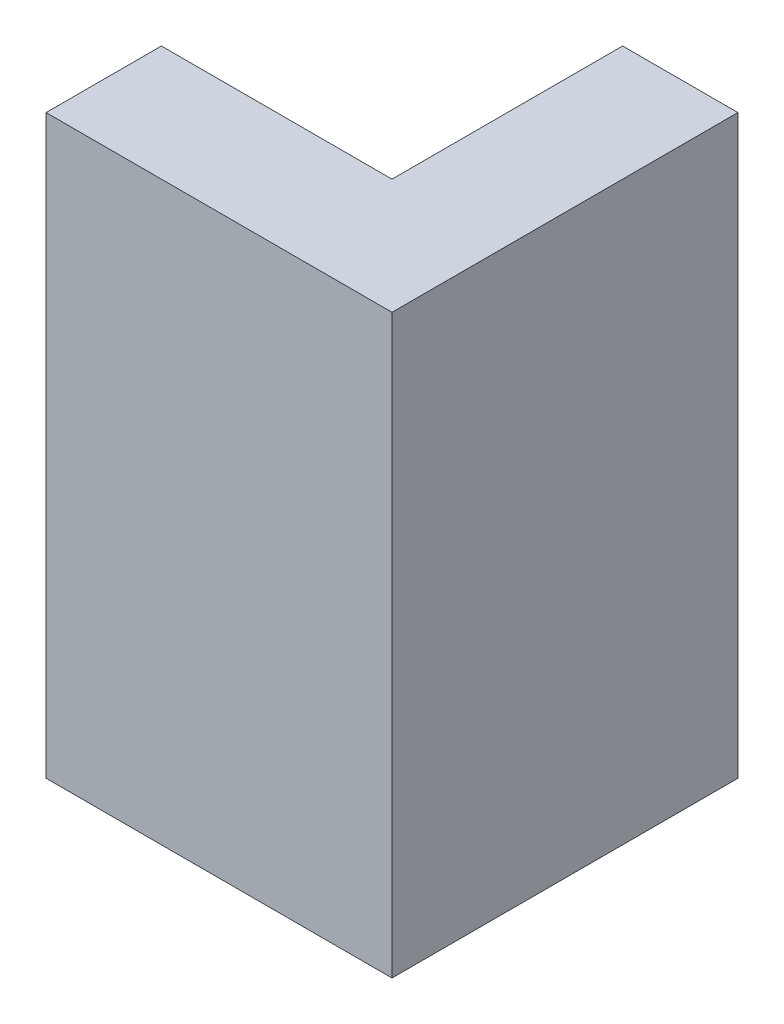
SolidWorks part; units mm, degrees
ref_plane "Front Plane" through (0, 0, 0) normal (0, 0, 1) x (1, 0, 0)
ref_plane "Top Plane" through (0, 0, 0) normal (0, 1, 0) x (1, 0, 0)
ref_plane "Right Plane" through (0, 0, 0) normal (1, 0, 0) x (0, 0, -1)
sketch "Sketch1" plane through (0, 0, 0) normal (0, 1, 0) x (1, 0, 0)
  line L0 (0, 0) -> (60, 0)
  line L1 (60, 0) -> (60, 60)
  line L3 (40, 74.7368) -> (39.9778, 74.7368)
  line L4 (40, 60) -> (40, 20)
  line L5 (40, 20) -> (0, 20)
  line L6 (0, 20) -> (0, 0)
  line L7 (60, 60) -> (40, 60)
  dimension "D1" = 20
  dimension "D2" = 60
  dimension "D3" = 20
  dimension "D4" = 90
  dimension "D5" = 60
extrude "Boss-Extrude1" add sketch "Sketch1" along normal blind 100 contours L1 L7 L4 L5 L6 L0
